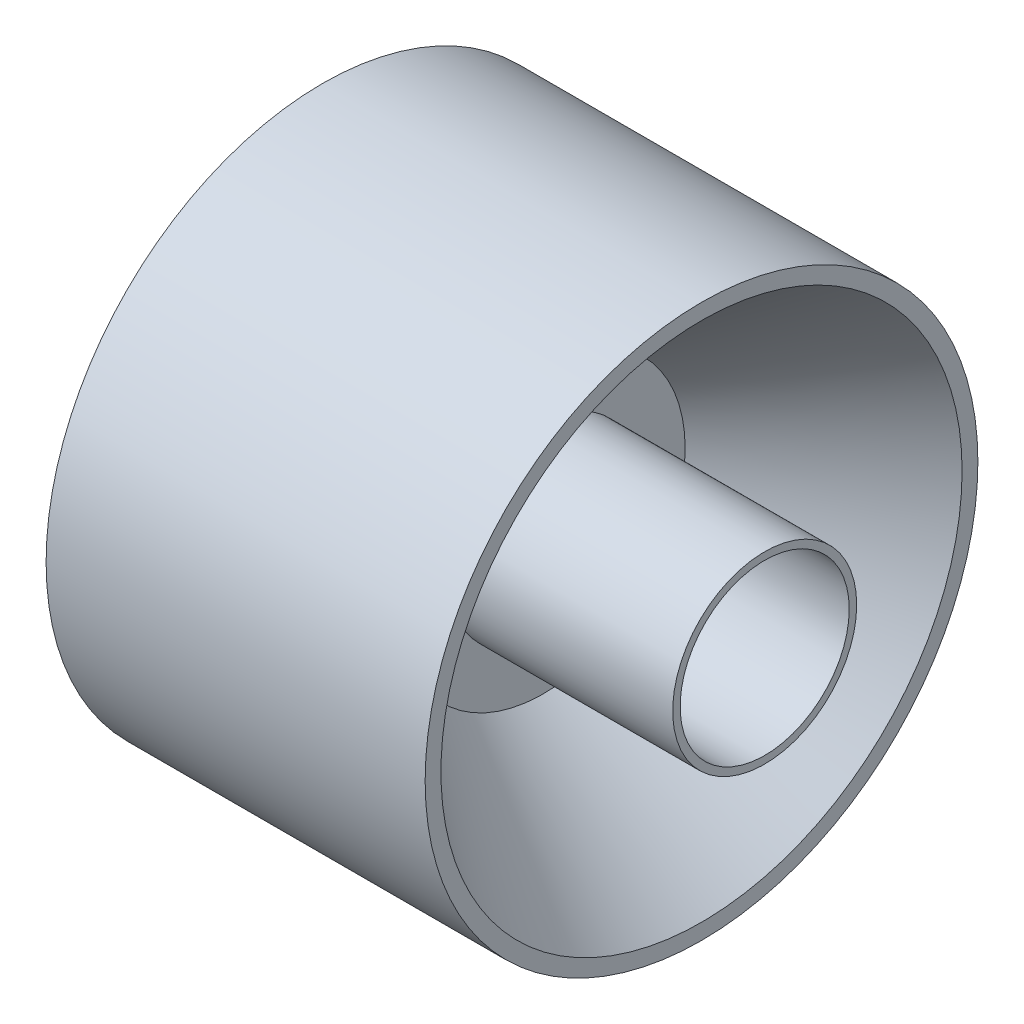
SolidWorks part; units mm, degrees
ref_plane "Front" through (0, 0, 0) normal (0, 0, 1) x (1, 0, 0)
ref_plane "Top" through (0, 0, 0) normal (0, 1, 0) x (1, 0, 0)
ref_plane "Right" through (0, 0, 0) normal (1, 0, 0) x (0, 0, -1)
sketch "Sketch1" plane through (0, 0, 0) normal (1, 0, 0) x (0, 0, -1)
  circle A0 centre (0, 0) radius 55.5625
  dimension "D1" = 111.125
extrude "Boss-Extrude1" add sketch "Sketch1" along normal blind 76.2
sketch "Sketch2" plane through (76.2, 0, 0) normal (1, 0, 0) x (0, 0, -1)
  circle A0 centre (0, 0) radius 52.3875
  circle A1 centre (0, 0) radius 55.5625 construction
  dimension "D1" = 3.175
extrude "Cut-Extrude1" cut sketch "Sketch2" against normal blind 31.75 draft 37
sketch "Sketch3" plane through (0, 0, 0) normal (-1, 0, 0) x (0, 0, 1)
  circle A0 centre (0, 0) radius 52.3875
  circle A1 centre (0, 0) radius 55.5625 construction
  dimension "D1" = 3.175
extrude "Cut-Extrude2" cut sketch "Sketch3" against normal blind 31.75 draft 37
sketch "Sketch4" plane through (44.45, 0, 0) normal (1, 0, 0) x (0, 0, -1)
  circle A0 centre (0, 0) radius 17
  circle A1 centre (0, 0) radius 18.5
  dimension "D1" = 34
  dimension "D2" = 1.5
extrude "Boss-Extrude2" add sketch "Sketch4" along normal blind 44.45
